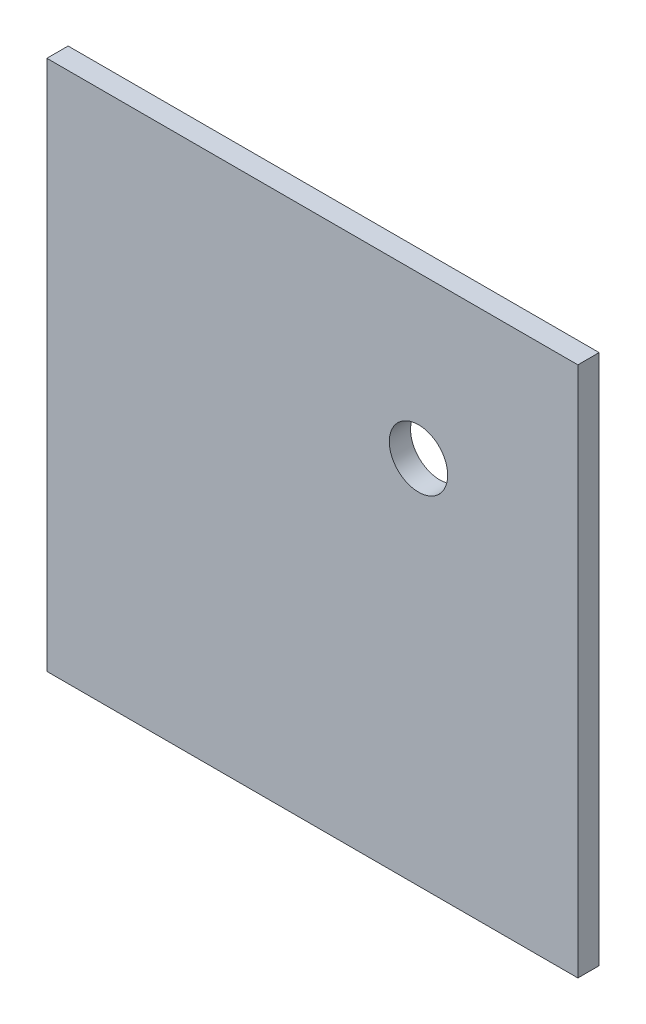
SolidWorks part; units mm, degrees
ref_plane "Front Plane" through (0, 0, 0) normal (0, 0, 1) x (1, 0, 0)
ref_plane "Top Plane" through (0, 0, 0) normal (0, 1, 0) x (1, 0, 0)
ref_plane "Right Plane" through (0, 0, 0) normal (1, 0, 0) x (0, 0, -1)
sketch "Sketch1" plane through (0, 0, 0) normal (0, 0, 1) x (1, 0, 0)
  line L1 (-50, -50) -> (50, -50)
  line L2 (-50, -50) -> (-50, 50)
  line L3 (-50, 50) -> (50, 50)
  line L4 (50, -50) -> (50, 50)
  line L5 (-50, -50) -> (50, 50) construction
  line L6 (-50, 50) -> (50, -50) construction
  point P0 (0, 0)
  dimension "D1" = 100
  dimension "D2" = 100
extrude "Boss-Extrude1" add sketch "Sketch1" along normal blind 4
sketch "Sketch2" plane through (0, 0, 0) normal (0, 0, -1) x (-1, 0, 0)
  line L0 (-50, 50) -> (50, 50) construction
  line L1 (-45, -45) -> (45, -45) construction
  line L2 (-45, -45) -> (-45, 45) construction
  line L3 (-45, 45) -> (45, 45) construction
  line L4 (45, -45) -> (45, 45) construction
  line L5 (50, 50) -> (50, -50) construction
  line L6 (50, -50) -> (-50, -50) construction
  line L7 (-50, -50) -> (-50, 50) construction
  circle A0 centre (45, 45) radius 4.75
  circle A1 centre (45, -45) radius 4.75
  circle A2 centre (-45, -45) radius 4.75
  circle A3 centre (-45, 45) radius 4.75
  dimension "D1" = 9.5
  dimension "D2" = 5
  dimension "D3" = 5
  dimension "D4" = 5
  dimension "D5" = 5
extrude "Cut-Extrude1" cut sketch "Sketch2" against normal blind 2
extrude "Cut-Extrude2" cut sketch "Sketch3" against normal through all
sketch "Sketch3" plane through (-38.4043, -79.6142, 4) normal (0, 0, 1) x (1, 0, 0)
  circle A3 centre (58.3876, 99.3452) radius 5.5
